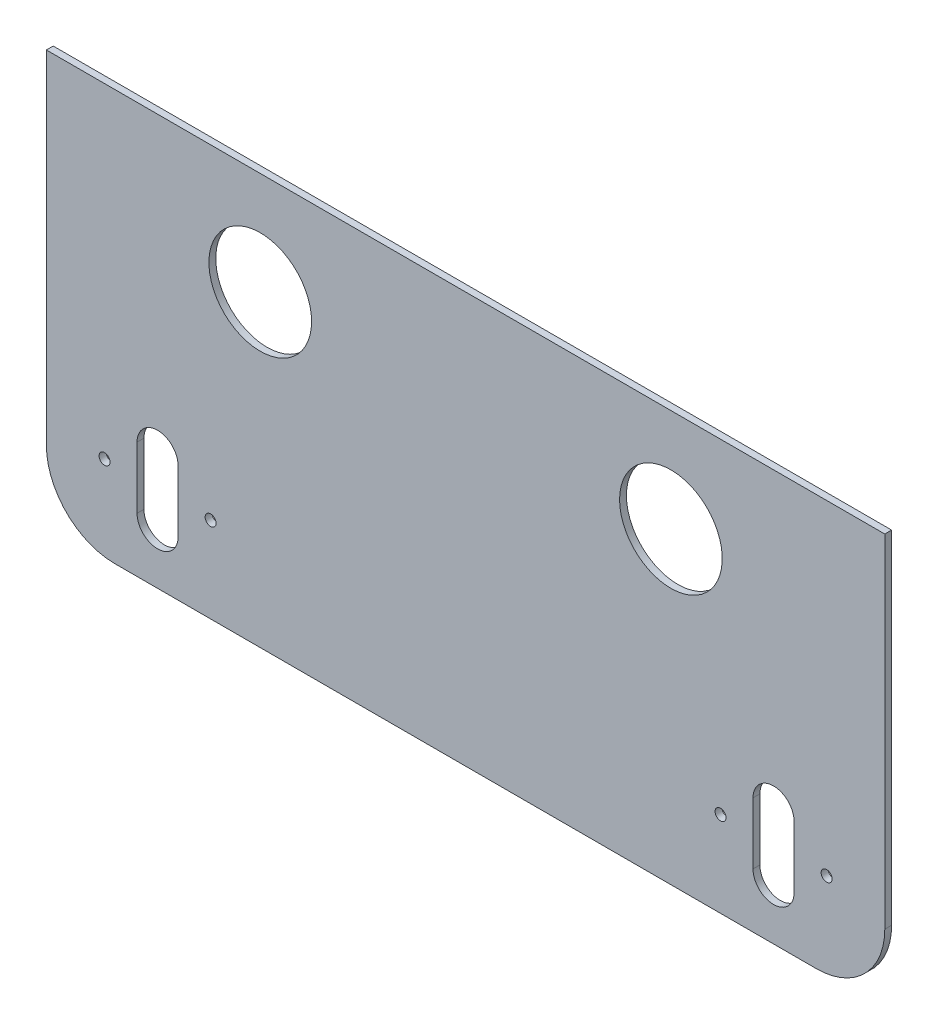
SolidWorks part; units mm, degrees
ref_plane "前视基准面" through (0, 0, 0) normal (0, 0, 1) x (1, 0, 0)
ref_plane "上视基准面" through (0, 0, 0) normal (0, 1, 0) x (1, 0, 0)
ref_plane "右视基准面" through (0, 0, 0) normal (1, 0, 0) x (0, 0, -1)
other "Configuration Table"
sketch "草图1" plane through (0, 0, 0) normal (0, 0, 1) x (1, 0, 0)
  line L0 (48.2911, 44.7063) -> (48.2911, -75.2937) construction
  line L1 (-74.2089, 44.7063) -> (170.7911, 44.7063)
  line L2 (-74.2089, 44.7063) -> (-74.2089, -75.2937)
  line L3 (-74.2089, -75.2937) -> (170.7911, -75.2937)
  line L4 (170.7911, 44.7063) -> (170.7911, -75.2937)
  line L5 (-74.2089, 14.7063) -> (170.7911, 14.7063) construction
  circle A0 centre (-11.7089, 14.7063) radius 15
  circle A1 centre (108.2911, 14.7063) radius 15
  dimension "D4" = 30
  dimension "D1" = 245
  dimension "D2" = 120
  dimension "D3" = 30
  dimension "D5" = 60
extrude "凸台-拉伸1" add sketch "草图1" along normal blind 2
fillet "圆角1" radius 20 1 edges at (170.7911, -75.2937, 1)
fillet "圆角2" radius 20 1 edges at (-74.2089, -75.2937, 1)
sketch "草图3" plane through (0, 0, 2) normal (0, 0, 1) x (1, 0, 0)
  line L0 (48.2911, 44.7063) -> (48.2911, -75.2937) construction
  line L1 (170.7911, 44.7063) -> (-74.2089, 44.7063) construction
  line L2 (-54.2089, -75.2937) -> (150.7911, -75.2937) construction
  line L3 (-74.2089, -50.2937) -> (170.7911, -50.2937) construction
  line L4 (-74.2089, 44.7063) -> (-74.2089, -55.2937) construction
  line L5 (170.7911, -55.2937) -> (170.7911, 44.7063) construction
  line L6 (-41.7089, -59.2937) -> (-41.7089, -41.2937) construction
  line L7 (-47.7089, -59.2937) -> (-47.7089, -41.2937)
  line L8 (-35.7089, -59.2937) -> (-35.7089, -41.2937)
  line L9 (138.2911, -59.2937) -> (138.2911, -41.2937) construction
  line L10 (144.2911, -59.2937) -> (144.2911, -41.2937)
  line L11 (132.2911, -59.2937) -> (132.2911, -41.2937)
  circle A0 centre (-41.7089, -50.2937) radius 15.5 construction
  circle A1 centre (-26.2089, -50.2937) radius 1.6
  circle A2 centre (-57.2089, -50.2937) radius 1.6
  circle A3 centre (153.7911, -50.2937) radius 1.6
  circle A4 centre (122.7911, -50.2937) radius 1.6
  arc A5 (-47.7089, -59.2937) -> (-35.7089, -59.2937) centre (-41.7089, -59.2937) ccw
  arc A6 (-35.7089, -41.2937) -> (-47.7089, -41.2937) centre (-41.7089, -41.2937) ccw
  arc A7 (144.2911, -59.2937) -> (132.2911, -59.2937) centre (138.2911, -59.2937) cw
  arc A8 (132.2911, -41.2937) -> (144.2911, -41.2937) centre (138.2911, -41.2937) cw
  point P23 (-41.7089, -50.2937)
  point P31 (138.2911, -50.2937)
  dimension "D2" = 31
  dimension "D3" = 3.2
  dimension "D5" = 6
  dimension "D1" = 25
  dimension "D4" = 90
  dimension "D6" = 18
extrude "切除-拉伸1" cut sketch "草图3" against normal blind 10
